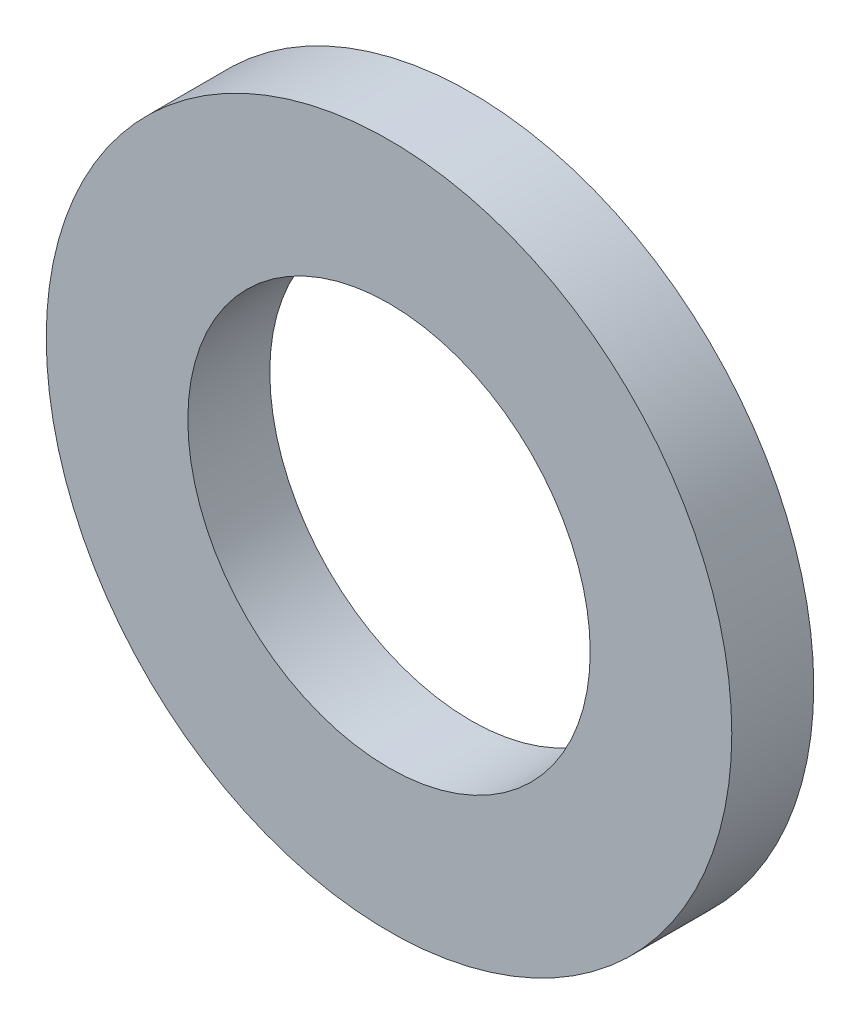
SolidWorks part; units mm, degrees
ref_plane "Front Plane" through (0, 0, 0) normal (0, 0, 1) x (1, 0, 0)
ref_plane "Top Plane" through (0, 0, 0) normal (0, 1, 0) x (1, 0, 0)
ref_plane "Right Plane" through (0, 0, 0) normal (1, 0, 0) x (0, 0, -1)
sketch "Sketch1" plane through (0, 0, 0) normal (0, 0, 1) x (1, 0, 0)
  circle A0 centre (0, 0) radius 4.6
  circle A1 centre (0, 0) radius 2.7
  dimension "OD" = 9.2
  dimension "ID1" = 5.4
extrude "Boss-Extrude1" add sketch "Sketch1" along normal blind 1.1
